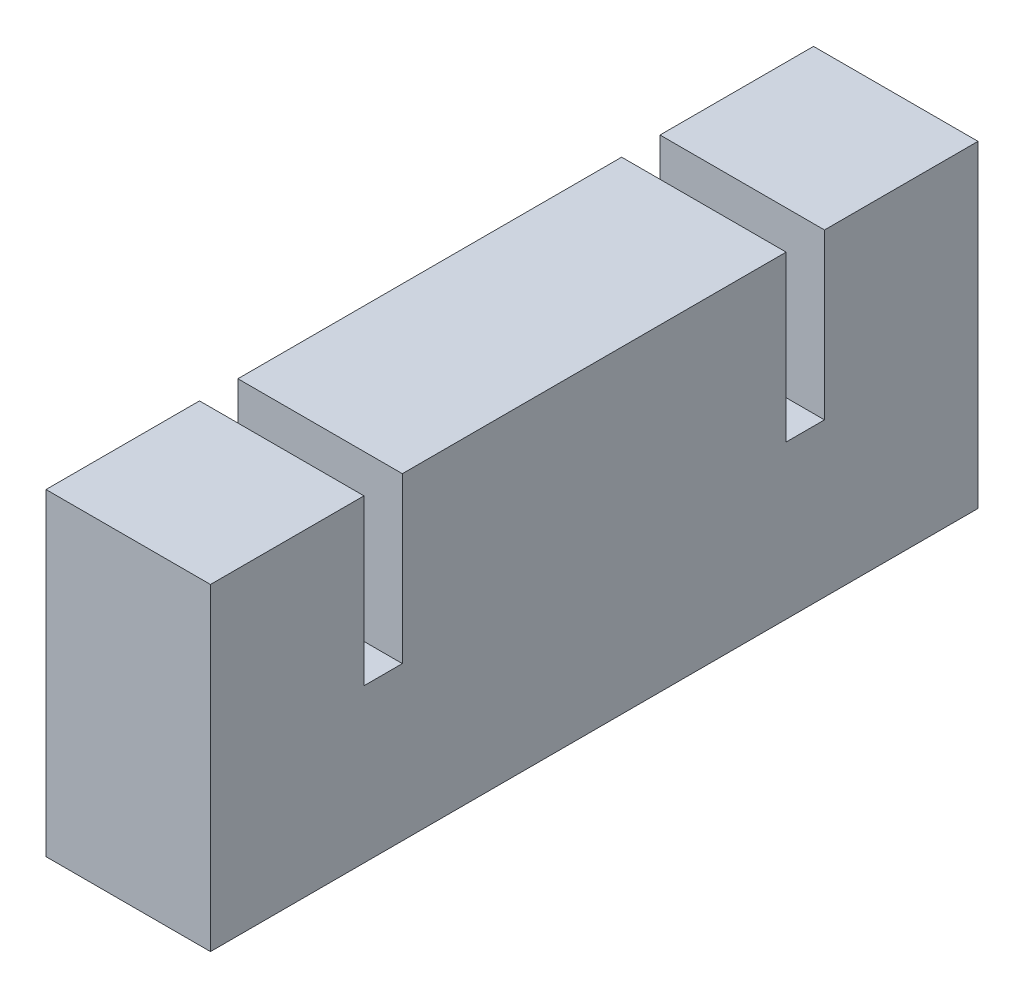
SolidWorks part; units mm, degrees
ref_plane "Front Plane" through (0, 0, 0) normal (0, 0, 1) x (1, 0, 0)
ref_plane "Top Plane" through (0, 0, 0) normal (0, 1, 0) x (1, 0, 0)
ref_plane "Right Plane" through (0, 0, 0) normal (1, 0, 0) x (0, 0, -1)
sketch "Sketch1" plane through (0, 0, 0) normal (0, 1, 0) x (1, 0, 0)
  line L1 (0, 0) -> (15, 0)
  line L2 (0, 0) -> (0, 70)
  line L3 (0, 70) -> (15, 70)
  line L4 (15, 0) -> (15, 70)
  dimension "D1" = 15
  dimension "D2" = 70
extrude "Boss-Extrude1" add sketch "Sketch1" along normal blind 14
sketch "Sketch2" plane through (0, 14, 0) normal (0, 1, 0) x (1, 0, 0)
  line L0 (0, 70) -> (0, 0) construction
  line L1 (0, 17.5) -> (15, 17.5)
  line L2 (0, 17.5) -> (0, 52.5)
  line L3 (0, 52.5) -> (15, 52.5)
  line L4 (15, 17.5) -> (15, 52.5)
  line L5 (15, 0) -> (15, 70) construction
  line L6 (0, 0) -> (15, 0) construction
  line L8 (15, 14) -> (0, 14)
  line L9 (15, 14) -> (15, 0)
  line L10 (15, 0) -> (0, 0)
  line L11 (0, 14) -> (0, 0)
  line L12 (0, 56) -> (15, 56)
  line L13 (0, 56) -> (0, 70)
  line L14 (0, 70) -> (15, 70)
  line L15 (15, 56) -> (15, 70)
  dimension "D1" = 35
  dimension "D2" = 17.5
  dimension "D3" = 14
  dimension "D4" = 14
extrude "Boss-Extrude2" add sketch "Sketch2" along normal blind 15
